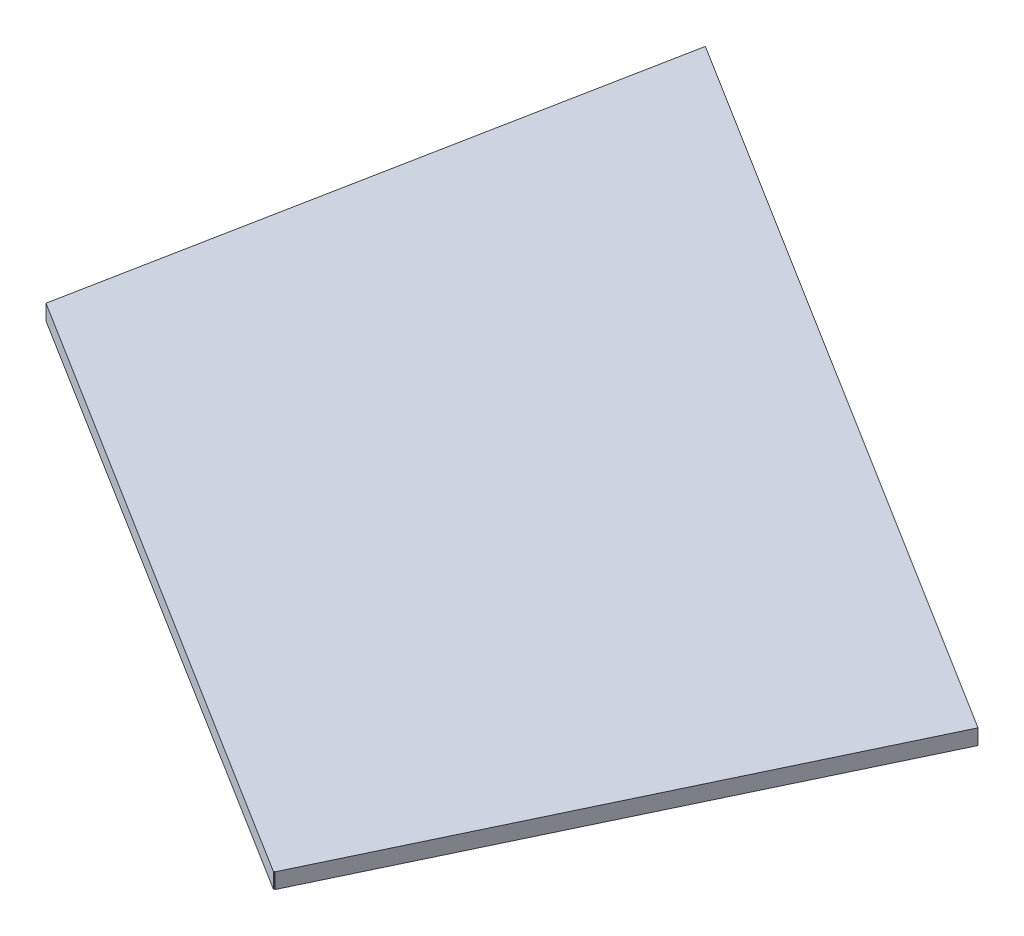
SolidWorks part; units mm, degrees
ref_plane "Plan de face" through (0, 0, 0) normal (0, 0, 1) x (1, 0, 0)
ref_plane "Plan de dessus" through (0, 0, 0) normal (0, 1, 0) x (1, 0, 0)
ref_plane "Plan de droite" through (0, 0, 0) normal (1, 0, 0) x (0, 0, -1)
sketch "Esquisse1" plane through (0, 0, 0) normal (0, 1, 0) x (1, 0, 0)
  line L0 (78.8824, -49.2806) -> (78.9323, -49.1682)
  line L1 (78.9323, -49.1682) -> (79.0217, -49.2239)
  line L2 (79.0217, -49.2239) -> (108.5552, 12.7931)
  line L3 (108.5552, 12.7931) -> (13.9704, 71.8835)
  line L4 (13.9704, 71.8835) -> (0, 0)
  line L5 (0, 0) -> (78.8824, -49.2806)
  point P6 (0, 0)
extrude "Boss.-Extru.1" add sketch "Esquisse1" along normal blind 2
